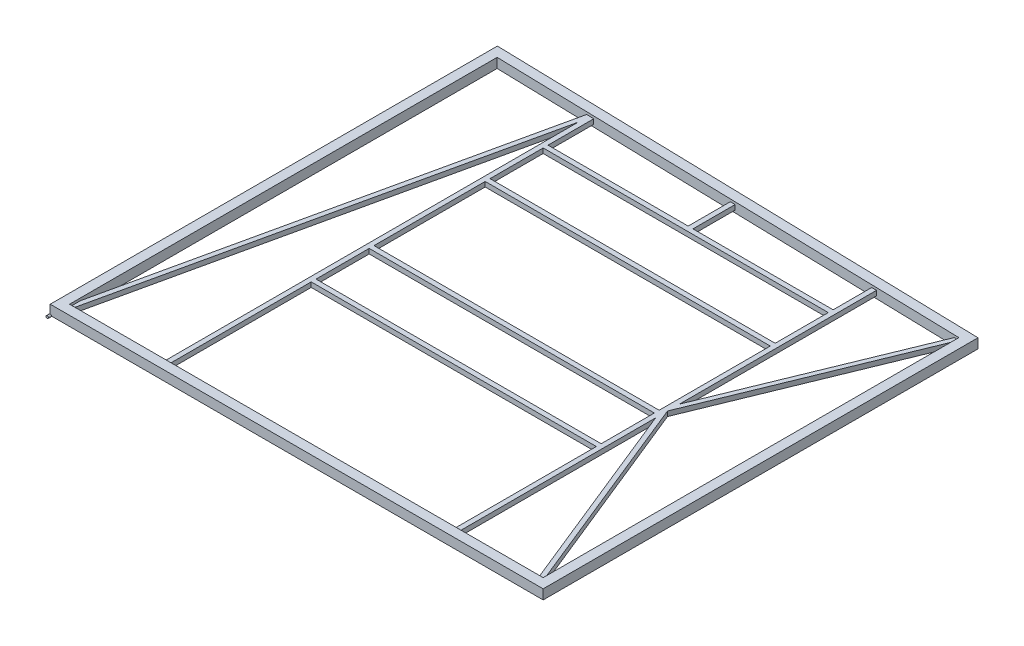
SolidWorks part; units mm, degrees
material "6063-T6"
ref_plane "Front Plane" through (0, 0, 0) normal (0, 0, 1) x (1, 0, 0)
ref_plane "Top Plane" through (0, 0, 0) normal (0, 1, 0) x (1, 0, 0)
ref_plane "Right Plane" through (0, 0, 0) normal (1, 0, 0) x (0, 0, -1)
sketch "Sketch1" plane through (0, 0, 0) normal (0, 1, 0) x (1, 0, 0)
  line L0 (0, 2298.7) -> (0, 0)
  line L1 (0, 0) -> (2540, 0)
  line L2 (2540, 0) -> (2540, 2235.2)
  line L3 (2540, 2235.2) -> (0, 2298.7)
  dimension "D1" = 2235.2
  dimension "D2" = 2540
  dimension "D3" = 2298.7
ref_plane "Plane1" through (0, 0, -1016) normal (0, 0, 1) x (1, 0, 0)
sketch "Sketch2" plane through (0, 0, -1016) normal (0, 0, 1) x (1, 0, 0)
  line L0 (-22.225, 22.225) -> (-22.225, -22.225)
  line L1 (-25.4, 25.4) -> (25.4, 25.4)
  line L2 (-25.4, 25.4) -> (-25.4, -25.4)
  line L3 (-25.4, -25.4) -> (25.4, -25.4)
  line L4 (25.4, 25.4) -> (25.4, -25.4)
  line L5 (-25.4, 25.4) -> (25.4, -25.4) construction
  line L6 (-25.4, -25.4) -> (25.4, 25.4) construction
  line L7 (-22.225, -22.225) -> (22.225, -22.225)
  line L8 (22.225, 22.225) -> (22.225, -22.225)
  line L9 (-22.225, 22.225) -> (22.225, 22.225)
  point P0 (0, 0)
  dimension "D1" = 50.8
  dimension "D2" = 50.8
  dimension "D3" = 3.175
sweep "Sweep1" add profiles "Sketch2" path "Sketch1"
sketch "Sketch3" plane through (0, 0, -25.4) normal (0, 0, -1) x (-1, 0, 0)
  line L0 (-520.7, -12.7) -> (-520.7, 12.7)
  line L1 (-2044.7, -12.7) -> (-2070.1, -12.7)
  line L2 (-2044.7, -12.7) -> (-2044.7, 12.7)
  line L3 (-2044.7, 12.7) -> (-2070.1, 12.7)
  line L4 (-2070.1, -12.7) -> (-2070.1, 12.7)
  line L5 (-2044.7, -12.7) -> (-2070.1, 12.7) construction
  line L6 (-2044.7, 12.7) -> (-2070.1, -12.7) construction
  line L7 (-2514.6, 25.4) -> (-2514.6, -25.4) construction
  line L8 (-2066.925, -9.525) -> (-2066.925, 9.525)
  line L9 (-2047.875, 9.525) -> (-2066.925, 9.525)
  line L10 (-2047.875, -9.525) -> (-2047.875, 9.525)
  line L11 (-2047.875, -9.525) -> (-2066.925, -9.525)
  line L12 (-2514.6, -25.4) -> (-25.4, -25.4) construction
  line L17 (-520.7, -12.7) -> (-546.1, -12.7)
  line L18 (-546.1, -12.7) -> (-546.1, 12.7)
  line L23 (-520.7, 12.7) -> (-546.1, 12.7)
  line L24 (-542.925, -9.525) -> (-542.925, 9.525)
  line L25 (-523.875, 9.525) -> (-542.925, 9.525)
  line L26 (-523.875, -9.525) -> (-523.875, 9.525)
  line L27 (-523.875, -9.525) -> (-542.925, -9.525)
  line L28 (-25.4, 25.4) -> (-25.4, -25.4) construction
  point P0 (-2057.4, 0)
  point P5 (-533.4, 12.7)
  point P20 (-2514.6, 0)
  dimension "D1" = 25.4
  dimension "D2" = 25.4
  dimension "D3" = 25.4
  dimension "D5" = 457.2
  dimension "D6" = 2
  dimension "D7" = 508
  dimension "D4" = 3.175
extrude "Boss-Extrude1" add sketch "Sketch3" along normal up to surface (2196.1396 mm away)
sketch "Sketch4" plane through (546.1, 0, 0) normal (1, 0, 0) x (0, 0, -1)
  line L0 (2259.6396, -12.7) -> (25.4, -12.7) construction
  line L1 (800.1, 12.7) -> (774.7, 12.7)
  line L2 (800.1, 12.7) -> (800.1, -12.7)
  line L3 (800.1, -12.7) -> (774.7, -12.7)
  line L4 (774.7, 12.7) -> (774.7, -12.7)
  line L5 (800.1, 12.7) -> (774.7, -12.7) construction
  line L6 (800.1, -12.7) -> (774.7, 12.7) construction
  line L7 (25.4, 12.7) -> (25.4, -12.7) construction
  line L8 (1104.9, 12.7) -> (1079.5, 12.7)
  line L9 (1104.9, 12.7) -> (1104.9, -12.7)
  line L10 (1104.9, -12.7) -> (1079.5, -12.7)
  line L11 (1079.5, 12.7) -> (1079.5, -12.7)
  line L12 (1104.9, 12.7) -> (1079.5, -12.7) construction
  line L13 (1104.9, -12.7) -> (1079.5, 12.7) construction
  line L14 (796.925, 9.525) -> (796.925, -9.525)
  line L15 (2259.6396, 12.7) -> (25.4, 12.7) construction
  line L16 (1714.5, 12.7) -> (1689.1, 12.7)
  line L17 (1714.5, 12.7) -> (1714.5, -12.7)
  line L18 (1714.5, -12.7) -> (1689.1, -12.7)
  line L19 (1689.1, 12.7) -> (1689.1, -12.7)
  line L20 (1714.5, 12.7) -> (1689.1, -12.7) construction
  line L21 (1714.5, -12.7) -> (1689.1, 12.7) construction
  line L22 (2019.3, 12.7) -> (1993.9, 12.7)
  line L23 (2019.3, 12.7) -> (2019.3, -12.7)
  line L24 (2019.3, -12.7) -> (1993.9, -12.7)
  line L25 (1993.9, 12.7) -> (1993.9, -12.7)
  line L26 (2019.3, 12.7) -> (1993.9, -12.7) construction
  line L27 (2019.3, -12.7) -> (1993.9, 12.7) construction
  line L28 (796.925, -9.525) -> (777.875, -9.525)
  line L29 (777.875, 9.525) -> (777.875, -9.525)
  line L30 (796.925, 9.525) -> (777.875, 9.525)
  line L31 (1101.725, 9.525) -> (1101.725, -9.525)
  line L32 (1101.725, -9.525) -> (1082.675, -9.525)
  line L33 (1082.675, 9.525) -> (1082.675, -9.525)
  line L34 (1101.725, 9.525) -> (1082.675, 9.525)
  line L35 (1711.325, 9.525) -> (1692.275, 9.525)
  line L36 (1692.275, 9.525) -> (1692.275, -9.525)
  line L37 (1711.325, -9.525) -> (1692.275, -9.525)
  line L38 (1711.325, 9.525) -> (1711.325, -9.525)
  line L39 (2016.125, 9.525) -> (1997.075, 9.525)
  line L40 (1997.075, 9.525) -> (1997.075, -9.525)
  line L41 (2016.125, -9.525) -> (1997.075, -9.525)
  line L42 (2016.125, 9.525) -> (2016.125, -9.525)
  point P0 (787.4, 0)
  point P7 (1092.2, 0)
  point P16 (1701.8, 0)
  point P21 (2006.6, 0)
  dimension "D1" = 25.4
  dimension "D2" = 25.4
  dimension "D3" = 304.8
  dimension "D4" = 762
  dimension "D5" = 25.4
  dimension "D6" = 25.4
  dimension "D7" = 304.8
  dimension "D8" = 609.6
  dimension "D9" = 3.175
  dimension "D10" = 3.175
  dimension "D11" = 3.175
  dimension "D12" = 3.175
extrude "Boss-Extrude2" add sketch "Sketch4" along normal up to surface (1498.6 mm away) up to face at (2044.7, 0, -1123.7873)
sketch "Sketch5" plane through (0, 0, -25.4) normal (0, 0, -1) x (-1, 0, 0)
  line L1 (-12.7, -12.7) -> (-38.1, -12.7)
  line L2 (-12.7, -12.7) -> (-12.7, 12.7)
  line L3 (-12.7, 12.7) -> (-38.1, 12.7)
  line L4 (-38.1, -12.7) -> (-38.1, 12.7)
  line L5 (-12.7, -12.7) -> (-38.1, 12.7) construction
  line L6 (-12.7, 12.7) -> (-38.1, -12.7) construction
  line L7 (-520.7, 12.7) -> (-546.1, 12.7) construction
  line L8 (-546.1, -12.7) -> (-520.7, -12.7) construction
  line L9 (-15.875, -9.525) -> (-15.875, 9.525)
  line L10 (-15.875, 9.525) -> (-34.925, 9.525)
  line L11 (-34.925, -9.525) -> (-34.925, 9.525)
  line L12 (-15.875, -9.525) -> (-34.925, -9.525)
  line L13 (-25.4, 25.4) -> (-25.4, -25.4) construction
  point P0 (-25.4, 0)
  point P16 (-25.4, 0)
  dimension "D1" = 25.4
  dimension "D2" = 3.175
sketch "Sketch6" plane through (0, 25.4, 0) normal (0, 1, 0) x (1, 0, 0)
  line L0 (25.4, 25.4) -> (520.7, 2260.2746)
sweep "Sweep2" add profiles "Sketch5" path "Sketch6"
sketch "Sketch11" plane through (0, 0, -2019.3) normal (0, 0, -1) x (-1, 0, 0)
  line L0 (-2044.7, -12.7) -> (-546.1, -12.7) construction
  line L1 (-1282.7, -12.7) -> (-1308.1, -12.7)
  line L2 (-1282.7, -12.7) -> (-1282.7, 12.7)
  line L3 (-1282.7, 12.7) -> (-1308.1, 12.7)
  line L4 (-1308.1, -12.7) -> (-1308.1, 12.7)
  line L5 (-1282.7, -12.7) -> (-1308.1, 12.7) construction
  line L6 (-1282.7, 12.7) -> (-1308.1, -12.7) construction
  line L7 (-2044.7, 12.7) -> (-546.1, 12.7) construction
  line L9 (-1285.875, -9.525) -> (-1285.875, 9.525)
  line L10 (-1285.875, 9.525) -> (-1304.925, 9.525)
  line L11 (-1304.925, -9.525) -> (-1304.925, 9.525)
  line L12 (-1285.875, -9.525) -> (-1304.925, -9.525)
  line L13 (-2044.7, 12.7) -> (-546.1, 12.7) construction
  point P12 (-1295.4, 12.7)
  point P20 (-1295.4, 0)
  dimension "D1" = 25.4
  dimension "D2" = 3.175
extrude "Boss-Extrude3" add sketch "Sketch11" along normal up to surface (221.2896 mm away)
sketch "Sketch13" plane through (0, 0, -25.4) normal (0, 0, -1) x (-1, 0, 0)
  line L0 (-2514.6, 25.4) -> (-2514.6, -25.4) construction
  line L1 (-2489.2, -12.7) -> (-2514.6, -12.7)
  line L2 (-2489.2, -12.7) -> (-2489.2, 12.7)
  line L3 (-2489.2, 12.7) -> (-2514.6, 12.7)
  line L4 (-2514.6, -12.7) -> (-2514.6, 12.7)
  line L5 (-2489.2, -12.7) -> (-2514.6, 12.7) construction
  line L6 (-2489.2, 12.7) -> (-2514.6, -12.7) construction
  line L7 (-2492.375, -9.525) -> (-2492.375, 9.525)
  line L8 (-2492.375, 9.525) -> (-2511.425, 9.525)
  line L9 (-2511.425, -9.525) -> (-2511.425, 9.525)
  line L10 (-2492.375, -9.525) -> (-2511.425, -9.525)
  point P0 (-2501.9, 0)
  point P8 (-2514.6, 0)
  dimension "D1" = 25.4
  dimension "D2" = 25.4
  dimension "D3" = 3.175
sketch "Sketch14" plane through (0, 25.4, 0) normal (0, 1, 0) x (1, 0, 0)
  line L0 (2514.6, 25.4) -> (2070.1, 1123.4698)
  line L1 (2070.1, 2221.5396) -> (2070.1, 25.4) construction
  line L2 (2070.1, 1123.4698) -> (2514.6, 2210.4271)
sweep "Sweep6" add profiles "Sketch13" path "Sketch14"
ref_plane "NORMAL PIN PLANE" through (0, 0, -2324.7429) normal (0, 0, 1) x (1, 0, 0)
sketch "Sketch15" plane through (0, 0, -2324.7429) normal (0, 0, 1) x (1, 0, 0)
  circle A0 centre (-25.4, -25.4) radius 6.35
  dimension "D1" = 12.7
extrude "Boss-Extrude4" add sketch "Sketch15" along normal mid plane 31.75
sketch "Sketch16" plane through (0, 0, 25.4) normal (0, 0, 1) x (1, 0, 0)
  circle A0 centre (-25.4, -25.4) radius 6.35
  dimension "D1" = 12.7
extrude "Boss-Extrude5" add sketch "Sketch16" along normal mid plane 31.75
